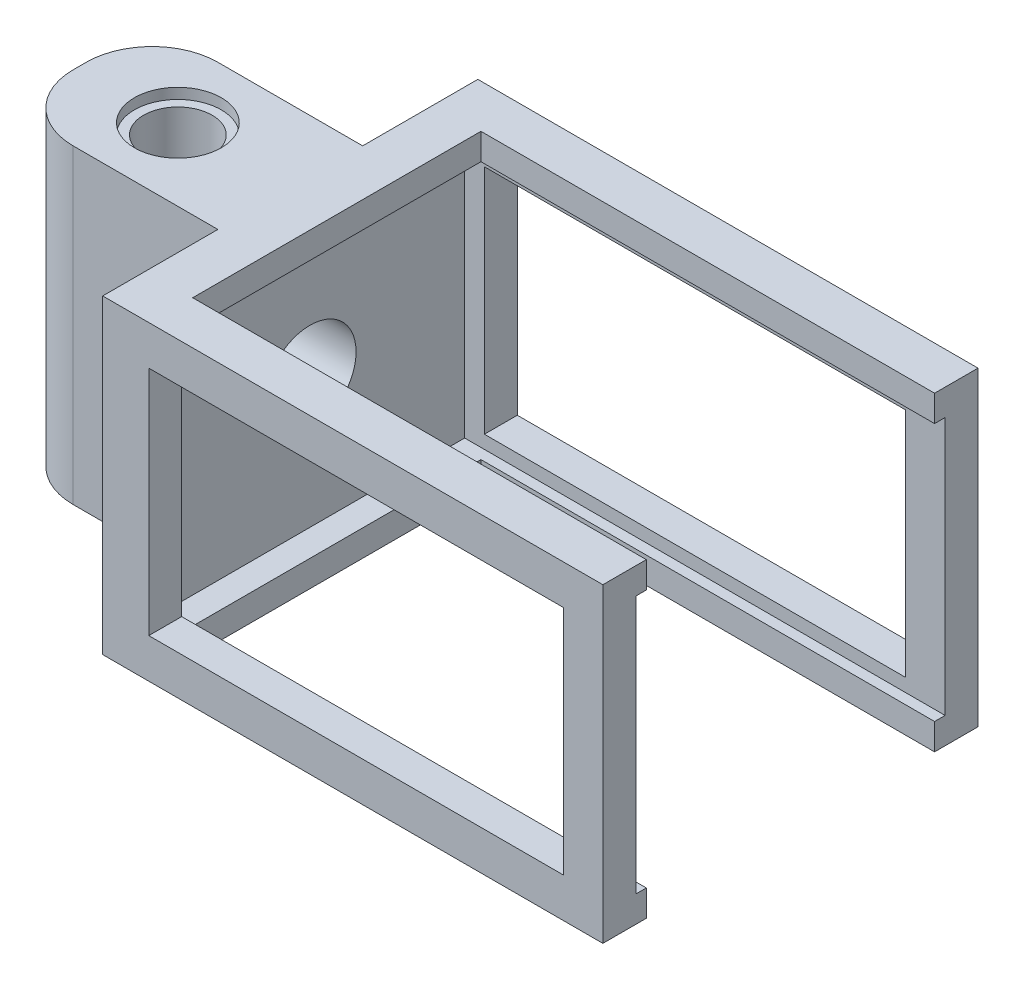
SolidWorks part; units mm, degrees
ref_plane "Front Plane" through (0, 0, 0) normal (0, 0, 1) x (1, 0, 0)
ref_plane "Top Plane" through (0, 0, 0) normal (0, 1, 0) x (1, 0, 0)
ref_plane "Right Plane" through (0, 0, 0) normal (1, 0, 0) x (0, 0, -1)
sketch "Sketch2" plane through (0, 0, 0) normal (0, 0, 1) x (1, 0, 0)
  line L1 (0, 0) -> (38, 0)
  line L2 (0, 0) -> (0, 23.6)
  line L3 (0, 23.6) -> (38, 23.6)
  line L4 (38, 0) -> (38, 23.6)
  dimension "D1" = 23.6
  dimension "D2" = 38
extrude "Boss-Extrude2" add sketch "Sketch2" along normal blind 2.5
sketch "Sketch3" plane through (0, 0, 2.5) normal (0, 0, 1) x (1, 0, 0)
  line L0 (38, 23.6) -> (38, 20.6) construction
  line L1 (38, 0) -> (38, 23.6) construction
  line L2 (38, 0) -> (38, 3) construction
  line L3 (0, 11.8) -> (3, 11.8) construction
  line L4 (0, 23.6) -> (0, 0) construction
  line L6 (38, 20.6) -> (3, 20.6)
  line L7 (38, 20.6) -> (38, 3)
  line L8 (38, 3) -> (3, 3)
  line L9 (3, 20.6) -> (3, 3)
  dimension "D1" = 3
  dimension "D2" = 3
  dimension "D3" = 3
extrude "Cut-Extrude2" cut sketch "Sketch3" against normal blind 2.5
sketch "Sketch5" plane through (0, 0, 2.5) normal (0, 0, 1) x (1, 0, 0)
  line L0 (38, 20.6) -> (38, 23.6) construction
  line L1 (0, 23.6) -> (38, 23.6)
  line L2 (0, 23.6) -> (0, 21.6)
  line L3 (0, 21.6) -> (38, 21.6)
  line L4 (38, 23.6) -> (38, 21.6)
  line L5 (0, 23.6) -> (0, 0) construction
  line L6 (38, 0) -> (0, 0)
  line L7 (38, 0) -> (38, 2)
  line L8 (38, 2) -> (0, 2)
  line L9 (0, 0) -> (0, 2)
  line L10 (0, 0) -> (1.5, 0) construction
  line L11 (0, 0) -> (1.5, 0)
  line L12 (0, 0) -> (0, 23.6)
  line L13 (0, 23.6) -> (1.5, 23.6)
  line L14 (1.5, 0) -> (1.5, 23.6)
  line L15 (0, 11.8) -> (1.5, 11.8) construction
  line M4 (38, 0) -> (38, 3)
  line M8 (38, 20.6) -> (38, 23.6)
  line M9 (38, 23.6) -> (0, 23.6)
  line M10 (0, 23.6) -> (0, 0)
  line M11 (0, 0) -> (38, 0)
  dimension "D1" = 2
  dimension "D2" = 2
  dimension "D3" = 1.5
extrude "Boss-Extrude3" add sketch "Sketch5" along normal blind 26 contours L14 L3 M8 M9 | L3 L14 L1 M10 | L8 L14 L3 M10 | L14 L8 M11 M10 | L14 L6 L8 M4
sketch "Sketch7" plane through (0, 2, 0) normal (0, 1, 0) x (1, 0, 0)
  line L0 (1.5, -28.5) -> (1.5, -2.5) construction
  line L1 (38, -28.5) -> (1.5, -28.5)
  line L2 (38, -28.5) -> (38, -26)
  line L3 (38, -26) -> (1.5, -26)
  line L4 (1.5, -28.5) -> (1.5, -26)
  dimension "D1" = 2.5
extrude "Boss-Extrude5" add sketch "Sketch7" along normal blind 1
sketch "Sketch10" plane through (0, 21.6, 0) normal (0, -1, 0) x (1, 0, 0)
  line L0 (38, 28.5) -> (38, 2.5) construction
  line L1 (1.5, 28.5) -> (38, 28.5)
  line L2 (1.5, 28.5) -> (1.5, 26)
  line L3 (1.5, 26) -> (38, 26)
  line L4 (38, 28.5) -> (38, 26)
  line L5 (25.4025, 26) -> (25.4025, 28.5)
  line M3 (38, 2.5) -> (38, 28.5)
  line M4 (38, 28.5) -> (1.5, 28.5)
  line M5 (1.5, 28.5) -> (1.5, 2.5)
  dimension "D1" = 2.5
extrude "Boss-Extrude6" add sketch "Sketch10" along normal blind 1 contours L5 L3 M3 M4 | L3 L5 L1 M5
sketch "Sketch11" plane through (1.5, 0, 0) normal (1, 0, 0) x (0, 0, -1)
  line L1 (-26, 3) -> (-28.5, 3)
  line L2 (-26, 3) -> (-26, 20.6)
  line L3 (-26, 20.6) -> (-28.5, 20.6)
  line L4 (-28.5, 3) -> (-28.5, 20.6)
extrude "Boss-Extrude7" add sketch "Sketch11" along normal blind 2
sketch "Sketch12" plane through (0, 21.6, 0) normal (0, -1, 0) x (-1, 0, 0)
  line L1 (12.2725, 16.9603) -> (-28.6118, 16.9603)
  line L2 (12.2725, 16.9603) -> (12.2725, 24.3169)
  line L3 (12.2725, 24.3169) -> (-28.6118, 24.3169)
  line L4 (-28.6118, 16.9603) -> (-28.6118, 24.3169)
ref_plane "Plane1" through (38, 21.6, 26) normal (0, 0, -1) x (-1, 0, 0)
sketch "Sketch15" plane through (0, 23.6, 0) normal (0, 1, 0) x (1, 0, 0)
  line L0 (34.1267, 0) -> (34.1267, -2.5) construction
  line L1 (38, 0) -> (0, 0) construction
  line L2 (34.5867, -28.5) -> (34.5867, -26) construction
  line L3 (38, -28.5) -> (0, -28.5) construction
  line L4 (44.4625, -26) -> (31.5375, -26) construction
  line L5 (0, -14.25) -> (3, -14.25) construction
  line L6 (0, -28.5) -> (0, 0) construction
  line L7 (38, -28.5) -> (38, 0) construction
  line L8 (34.1267, -2.5) -> (3.5372, -2.5)
  line L9 (34.1267, -2.5) -> (34.1267, -26)
  line L10 (34.1267, -26) -> (3.5372, -26)
  line L11 (3.5372, -2.5) -> (3.5372, -26)
  line L12 (3.5372, -2.5) -> (38, -2.5)
  line L13 (3.5372, -2.5) -> (3.5372, -26)
  line L14 (3.5372, -26) -> (38, -26)
  line L15 (38, -2.5) -> (38, -26)
  line M6 (38, -28.5) -> (38, 0)
  dimension "D1" = 2.5
  dimension "D2" = 3
extrude "Cut-Extrude4" cut sketch "Sketch15" against normal blind 30 contours L8 L11 L10 L9 | L9 L14 L12 M6
sketch "Sketch16" plane through (0, 3, 0) normal (0, 1, 0) x (1, 0, 0)
  line L0 (3, 0) -> (38, 0) construction
  line L1 (38, -2.5) -> (35, -2.5)
  line L2 (38, -2.5) -> (38, 0)
  line L3 (38, 0) -> (35, 0)
  line L4 (35, -2.5) -> (35, 0)
  dimension "D1" = 3
extrude "Boss-Extrude8" add sketch "Sketch16" along normal blind 20
sketch "Sketch17" plane through (0, 3, 0) normal (0, 1, 0) x (1, 0, 0)
  line L0 (38, -26) -> (3.5, -26) construction
  line L1 (38, -28.5) -> (35, -28.5)
  line L2 (38, -28.5) -> (38, -26)
  line L3 (38, -26) -> (35, -26)
  line L4 (35, -28.5) -> (35, -26)
  dimension "D1" = 3
extrude "Boss-Extrude9" add sketch "Sketch17" along normal blind 20
sketch "Sketch18" plane through (0, 23.6, 0) normal (0, 1, 0) x (1, 0, 0)
  line L0 (0, -14.25) -> (13.6, -14.25) construction
  line L1 (0, -28.5) -> (0, 0) construction
  circle A0 centre (13.6, -14.25) radius 3.69
  circle A1 centre (6.22, -14.25) radius 3.69
  circle A2 centre (-1.16, -14.25) radius 3.69
  circle A3 centre (-8.54, -14.25) radius 3.69
  dimension "D2" = 7.38
  dimension "D3" = 4
  dimension "D1" = 13.6
sketch "Sketch19" plane through (0, 0, 0) normal (-1, 0, 0) x (0, 0, 1)
  line L0 (28.5, 23.6) -> (0, 23.6) construction
  line L1 (14.25, 23.6) -> (8.75, 23.6)
  line L2 (14.25, 23.6) -> (14.25, 0)
  line L3 (14.25, 0) -> (8.75, 0)
  line L4 (8.75, 23.6) -> (8.75, 0)
  line L5 (28.5, 0) -> (0, 0) construction
  line L7 (14.25, 23.6) -> (19.75, 23.6)
  line L8 (14.25, 23.6) -> (14.25, 0)
  line L9 (14.25, 0) -> (19.75, 0)
  line L10 (19.75, 23.6) -> (19.75, 0)
  line M4 (0, 0) -> (28.5, 0)
  line M6 (28.5, 23.6) -> (0, 23.6)
  dimension "D1" = 5.5
  dimension "D2" = 5.5
extrude "Boss-Extrude10" add sketch "Sketch19" along normal blind 16 contours L10 L2 M6 M4 | L4 L2 M6 M4
sketch "Sketch20" plane through (0, 23.6, 0) normal (0, 1, 0) x (1, 0, 0)
  circle A0 centre (-8.54, -14.25) radius 2.6
  dimension "D1" = 5.2
extrude "Cut-Extrude6" cut sketch "Sketch20" against normal blind 30
sketch "Sketch21" plane through (0, 23.6, 0) normal (0, 1, 0) x (1, 0, 0)
  circle A0 centre (-8.54, -14.25) radius 3.3
  dimension "D1" = 6.6
extrude "Cut-Extrude7" cut sketch "Sketch21" against normal blind 0.8
sketch "Sketch22" plane through (0, 0, 0) normal (0, -1, 0) x (1, 0, 0)
  circle A0 centre (-8.54, 14.25) radius 3.3
  dimension "D1" = 6.6
extrude "Cut-Extrude8" cut sketch "Sketch22" against normal blind 0.8
fillet "Fillet1" radius 5 1 edges at (-16, 11.8, 8.75)
fillet "Fillet3" radius 5 1 edges at (-16, 11.8, 19.75)
sketch "Sketch23" plane through (0, 0, 26) normal (0, 0, -1) x (-1, 0, 0)
  line L1 (-3.5372, 21.6) -> (-38, 21.6)
  line L2 (-3.5372, 21.6) -> (-3.5372, 23.6)
  line L3 (-3.5372, 23.6) -> (-38, 23.6)
  line L4 (-38, 21.6) -> (-38, 23.6)
extrude "Boss-Extrude11" add sketch "Sketch23" along normal blind 0.8
sketch "Sketch24" plane through (0, 0, 2.5) normal (0, 0, 1) x (1, 0, 0)
  line L1 (3.5372, 21.6) -> (38, 21.6)
  line L2 (3.5372, 21.6) -> (3.5372, 23.6)
  line L3 (3.5372, 23.6) -> (38, 23.6)
  line L4 (38, 21.6) -> (38, 23.6)
extrude "Boss-Extrude12" add sketch "Sketch24" along normal blind 0.8
sketch "Sketch25" plane through (0, 0, 26) normal (0, 0, -1) x (-1, 0, 0)
  line L0 (-38, 21.6) -> (-38, 0) construction
  line L1 (-3.5372, 0) -> (-38, 0)
  line L2 (-3.5372, 0) -> (-3.5372, 2)
  line L3 (-3.5372, 2) -> (-38, 2)
  line L4 (-38, 0) -> (-38, 2)
  dimension "D1" = 2
extrude "Boss-Extrude13" add sketch "Sketch25" along normal blind 0.8
sketch "Sketch26" plane through (0, 0, 2.5) normal (0, 0, 1) x (1, 0, 0)
  line L0 (38, 0) -> (38, 21.6) construction
  line L1 (3.5372, 0) -> (38, 0)
  line L2 (3.5372, 0) -> (3.5372, 2)
  line L3 (3.5372, 2) -> (38, 2)
  line L4 (38, 0) -> (38, 2)
  dimension "D1" = 2
extrude "Boss-Extrude14" add sketch "Sketch26" along normal blind 0.8
sketch "Sketch27" plane through (1.5, 0, 0) normal (1, 0, 0) x (0, 0, -1)
  line L0 (-14.25, 2) -> (-14.25, 21.6)
  line L1 (-26, 2) -> (-2.5, 2) construction
  line L2 (-26, 21.6) -> (-2.5, 21.6) construction
  line L3 (-2.5, 11.8) -> (-26, 11.8)
  line L4 (-2.5, 2) -> (-2.5, 21.6) construction
  line L5 (-26, 21.6) -> (-26, 2) construction
  circle A0 centre (-14.25, 11.8) radius 3.5
  dimension "D1" = 7
extrude "Cut-Extrude9" cut sketch "Sketch27" against normal blind 6 contours L0 A0 L3 | L3 A0 L0 | L0 A0 L3 | L3 A0 L0
